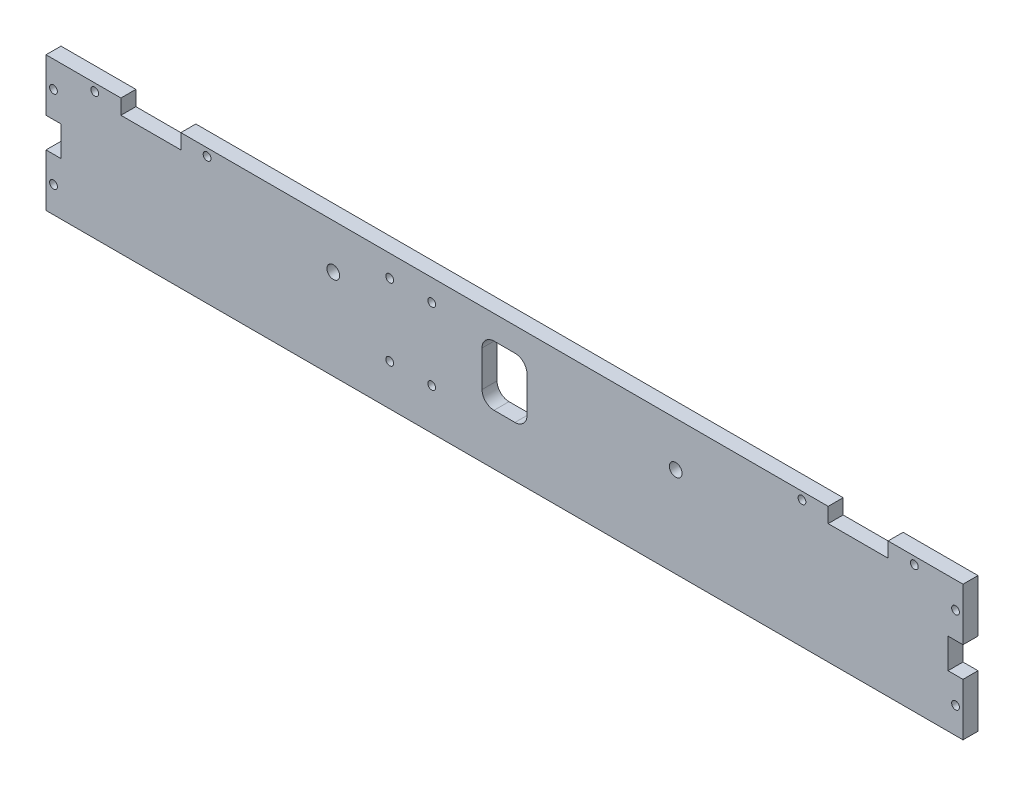
SolidWorks part; units mm, degrees
material "Pine"
ref_plane "Front Plane" through (0, 0, 0) normal (0, 0, 1) x (1, 0, 0)
ref_plane "Top Plane" through (0, 0, 0) normal (0, 1, 0) x (1, 0, 0)
ref_plane "Right Plane" through (0, 0, 0) normal (1, 0, 0) x (0, 0, -1)
ref_plane "Plane1" through (0, 0, 215.9) normal (0, 0, -1) x (-1, 0, 0)
sketch "Sketch1" plane through (0, 0, 215.9) normal (0, 0, -1) x (-1, 0, 0)
  line L0 (192.405, 21.59) -> (183.515, 21.59)
  line L1 (178.435, 26.67) -> (178.435, 41.91)
  line L2 (183.515, 46.99) -> (192.405, 46.99)
  line L3 (197.485, 41.91) -> (197.485, 26.67)
  line L4 (50.8, 57.15) -> (50.8, 50.8)
  line L5 (50.8, 50.8) -> (25.4, 50.8)
  line L6 (25.4, 50.8) -> (25.4, 57.15)
  line L7 (25.4, 57.15) -> (-6.35, 57.15)
  line L8 (-6.35, 57.15) -> (-6.35, 34.925)
  line L9 (-6.35, 34.925) -> (0, 34.925)
  line L10 (0, 34.925) -> (0, 22.225)
  line L11 (0, 22.225) -> (-6.35, 22.225)
  line L12 (-6.35, 22.225) -> (-6.35, 0)
  line L13 (-6.35, 0) -> (382.27, 0)
  line L14 (382.27, 0) -> (382.27, 22.225)
  line L15 (382.27, 22.225) -> (375.92, 22.225)
  line L16 (375.92, 22.225) -> (375.92, 34.925)
  line L17 (375.92, 34.925) -> (382.27, 34.925)
  line L18 (382.27, 34.925) -> (382.27, 57.15)
  line L19 (382.27, 57.15) -> (350.52, 57.15)
  line L20 (350.52, 57.15) -> (350.52, 50.8)
  line L21 (350.52, 50.8) -> (325.12, 50.8)
  line L22 (325.12, 50.8) -> (325.12, 57.15)
  line L23 (325.12, 57.15) -> (50.8, 57.15)
  circle A0 centre (379.095, 11.1125) radius 1.65
  circle A1 centre (-3.175, 11.1125) radius 1.65
  circle A2 centre (379.095, 46.0375) radius 1.65
  circle A3 centre (-3.175, 46.0375) radius 1.65
  arc A4 (183.515, 21.59) -> (178.435, 26.67) centre (183.515, 26.67) cw
  arc A5 (178.435, 41.91) -> (183.515, 46.99) centre (183.515, 41.91) cw
  arc A6 (192.405, 46.99) -> (197.485, 41.91) centre (192.405, 41.91) cw
  arc A7 (197.485, 26.67) -> (192.405, 21.59) centre (192.405, 26.67) cw
  circle A8 centre (314.0075, 53.975) radius 1.65
  circle A9 centre (61.9125, 53.975) radius 1.65
  circle A10 centre (361.6325, 53.975) radius 1.65
  circle A11 centre (14.2875, 53.975) radius 1.65
  circle A12 centre (260.51, 38.26) radius 2.7
  circle A13 centre (115.41, 38.26) radius 2.7
extrude "Boss-Extrude1" add sketch "Sketch1" against normal blind 6.35
sketch "Sketch2" plane through (0, 0, 222.25) normal (0, 0, 1) x (1, 0, 0)
  line L0 (-325.12, 57.15) -> (-50.8, 57.15) construction
  line L1 (-197.485, 26.67) -> (-197.485, 41.91) construction
  circle A0 centre (-218.821, 47.9552) radius 1.65
  circle A1 centre (-236.601, 47.9552) radius 1.65
  circle A2 centre (-236.601, 17.4752) radius 1.65
  circle A3 centre (-218.821, 17.4752) radius 1.65
  dimension "D2" = 3.3
  dimension "D1" = 9.1948
  dimension "D3" = 30.48
  dimension "D4" = 17.78
  dimension "D5" = 21.336
extrude "Cut-Extrude1" cut sketch "Sketch2" against normal up to next
